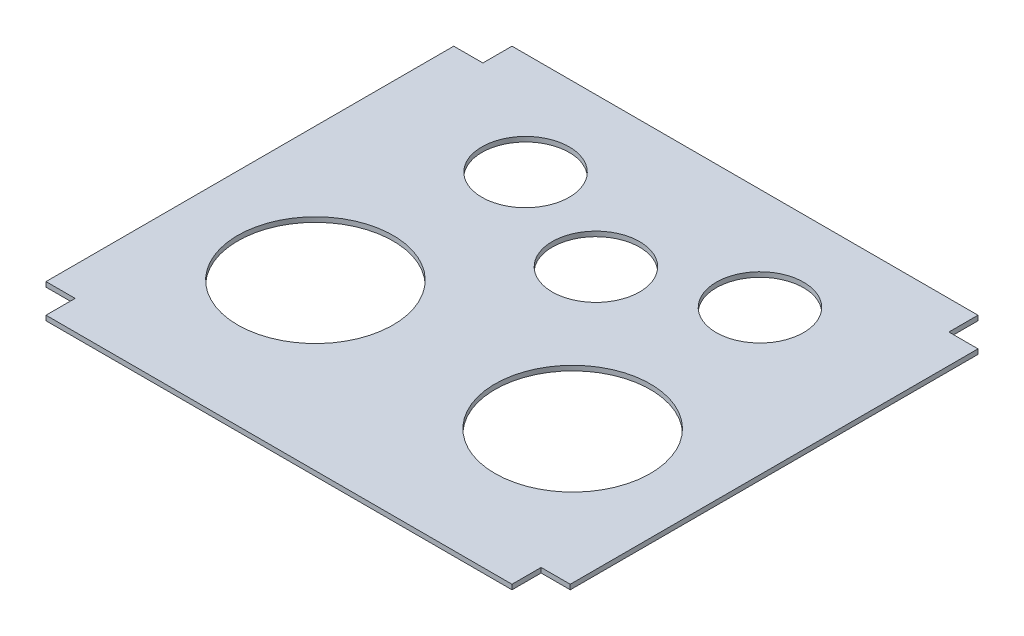
SolidWorks part; units mm, degrees
material "AISI 1020"
ref_plane "Front Plane" through (0, 0, 0) normal (0, 0, 1) x (1, 0, 0)
ref_plane "Top Plane" through (0, 0, 0) normal (0, 1, 0) x (1, 0, 0)
ref_plane "Right Plane" through (0, 0, 0) normal (1, 0, 0) x (0, 0, -1)
sketch "Sketch1" plane through (0, 0, 0) normal (0, 1, 0) x (1, 0, 0)
  line L0 (0, 0) -> (0, -38.1)
  line L1 (0, -38.1) -> (-609.6, -38.1)
  line L2 (-609.6, -38.1) -> (-609.6, 0)
  line L3 (-609.6, 0) -> (-647.7, 0)
  line L4 (-647.7, 0) -> (-647.7, 533.4)
  line L5 (-647.7, 533.4) -> (-609.6, 533.4)
  line L6 (-609.6, 533.4) -> (-609.6, 571.5)
  line L7 (-609.6, 571.5) -> (0, 571.5)
  line L8 (0, 571.5) -> (0, 533.4)
  line L9 (0, 533.4) -> (38.1, 533.4)
  line L10 (38.1, 533.4) -> (38.1, 0)
  line L11 (38.1, 0) -> (0, 0)
  line L12 (0, 0) -> (-609.6, 0) construction
  line L13 (-609.6, 533.4) -> (-609.6, 0) construction
  line L14 (-609.6, 533.4) -> (0, 533.4) construction
  line L15 (0, 533.4) -> (0, 0) construction
  line L16 (-609.6, -38.1) -> (-609.6, -63.5) construction
  line L17 (-609.6, -63.5) -> (0, -63.5) construction
  line L18 (0, -63.5) -> (0, -38.1) construction
  line L19 (-458.1141, 437.7198) -> (-151.4859, 437.7198) construction
  line L20 (-609.6, 376.4596) -> (0, 376.4596) construction
  line L21 (-473.075, 177.8) -> (-136.525, 177.8) construction
  line L22 (-304.8, 177.8) -> (-304.8, 0) construction
  line L23 (-304.8, 437.7198) -> (-304.8, 533.4) construction
  circle A0 centre (-473.075, 177.8) radius 101.6
  circle A1 centre (-473.075, 177.8) radius 177.8 construction
  circle A2 centre (-136.525, 177.8) radius 101.6
  circle A3 centre (-136.525, 177.8) radius 158.75 construction
  circle A4 centre (-304.8, 376.4596) radius 57.15
  circle A5 centre (-304.8, 376.4596) radius 82.55 construction
  circle A6 centre (-473.075, 177.8) radius 127 construction
  circle A7 centre (-136.525, 177.8) radius 127 construction
  circle A8 centre (-151.4859, 437.7198) radius 57.15
  circle A9 centre (-151.4859, 437.7198) radius 82.55 construction
  circle A10 centre (-458.1141, 437.7198) radius 57.15
  circle A11 centre (-458.1141, 437.7198) radius 82.55 construction
  dimension "D7" = 165.1
  dimension "D8" = 114.3
  dimension "D9" = 203.2
  dimension "D10" = 355.6
  dimension "D11" = 317.5
  dimension "D12" = 203.2
  dimension "D13" = 254
  dimension "D14" = 254
  dimension "D17" = 165.1
  dimension "D18" = 114.3
  dimension "D19" = 165.1
  dimension "D20" = 114.3
  dimension "D1" = 38.1
  dimension "D2" = 38.1
  dimension "D3" = 38.1
  dimension "D4" = 38.1
  dimension "D5" = 609.6
  dimension "D6" = 533.4
  dimension "D15" = 25.4
  dimension "D16" = 215.9
extrude "Boss-Extrude1" add sketch "Sketch1" along normal blind 6.35
equation "\"D2@Sketch1\"=\"D1@Sketch1\""
equation "\"D3@Sketch1\"=\"D1@Sketch1\""
equation "\"D4@Sketch1\"=\"D1@Sketch1\""
